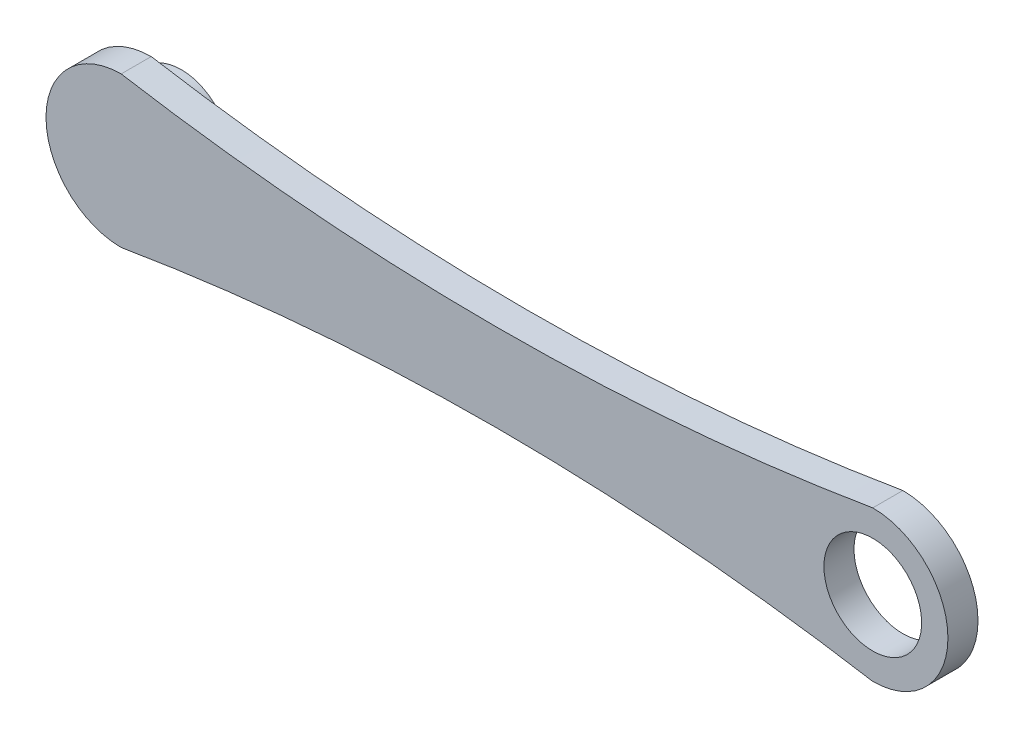
SolidWorks part; units mm, degrees
ref_plane "Front Plane" through (0, 0, 0) normal (0, 0, 1) x (1, 0, 0)
ref_plane "Top Plane" through (0, 0, 0) normal (0, 1, 0) x (1, 0, 0)
ref_plane "Right Plane" through (0, 0, 0) normal (1, 0, 0) x (0, 0, -1)
sketch "Sketch1" plane through (0, 0, 0) normal (0, 0, 1) x (1, 0, 0)
  line L0 (-125, 0) -> (125, 0) construction
  line L1 (-125, -25) -> (125, -25) construction
  line L3 (-125, 25) -> (125, 25) construction
  line L5 (-125, -25) -> (125, 25) construction
  line L6 (-125, 25) -> (125, -25) construction
  arc A0 (-125, 25) -> (-125, -25) centre (-125, 0) ccw
  arc A1 (125, -25) -> (125, 25) centre (125, 0) ccw
  arc A2 (-125, 25) -> (125, 25) centre (0, 764.51) ccw
  arc A3 (-125, -25) -> (125, -25) centre (0, -764.51) cw
  point P0 (0, 0)
  dimension "D4" = 25
  dimension "D3" = 750
  dimension "D1" = 250
  dimension "D2" = 50
extrude "Boss-Extrude1" add sketch "Sketch1" along normal blind 10
sketch "Sketch3" plane through (0, 0, 10) normal (0, 0, 1) x (1, 0, 0)
  circle A1 centre (125, 0) radius 16.25
  dimension "D2" = 32.5
  dimension "D1" = 125
sketch "Sketch2" plane through (0, 0, 0) normal (0, 0, -1) x (1, 0, 0)
  circle A0 centre (-125, 0) radius 16.25
  dimension "D2" = 125
  dimension "D1" = 32.5
extrude "Boss-Extrude2" add sketch "Sketch2" along normal blind 10
extrude "Cut-Extrude1" cut sketch "Sketch3" against normal blind 10
